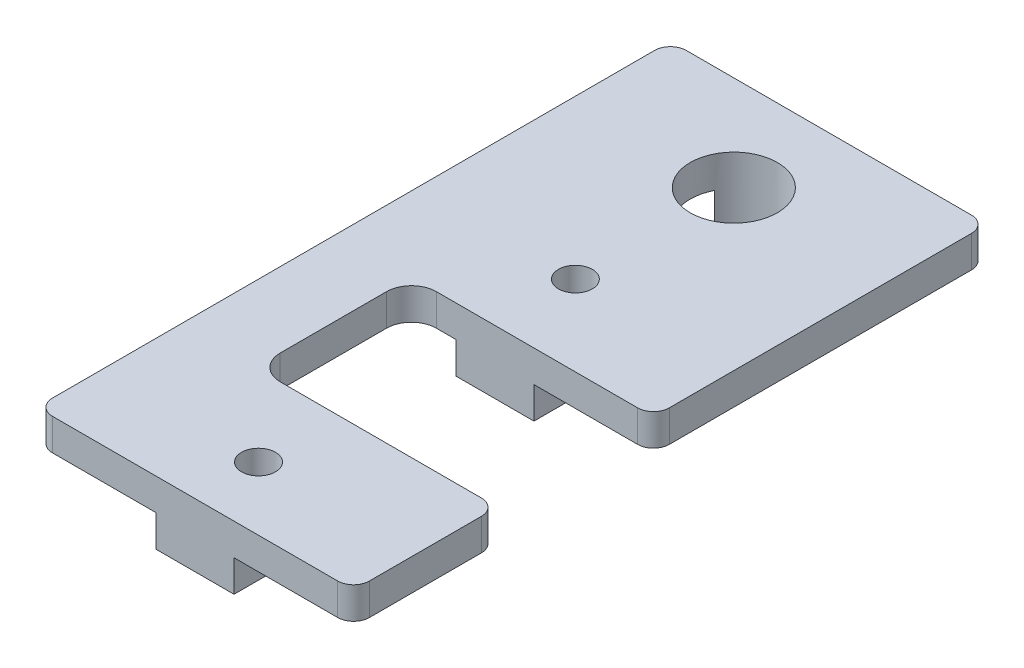
SolidWorks part; units mm, degrees
ref_plane "Front Plane" through (0, 0, 0) normal (0, 0, 1) x (1, 0, 0)
ref_plane "Top Plane" through (0, 0, 0) normal (0, 1, 0) x (1, 0, 0)
ref_plane "Right Plane" through (0, 0, 0) normal (1, 0, 0) x (0, 0, -1)
sketch "Sketch3" plane through (0, 0, 0) normal (0, 0, 1) x (1, 0, 0)
  line L1 (0, 0) -> (31.75, 0)
  line L2 (0, 0) -> (0, 3.175)
  line L3 (0, 3.175) -> (31.75, 3.175)
  line L4 (31.75, 0) -> (31.75, 3.175)
  line L5 (0, 0) -> (31.75, 3.175) construction
  line L6 (0, 3.175) -> (31.75, 0) construction
  line L7 (11.975, 0) -> (19.775, 0)
  line L8 (11.975, 0) -> (11.975, -3.175)
  line L9 (11.975, -3.175) -> (19.775, -3.175)
  line L10 (19.775, 0) -> (19.775, -3.175)
  line L11 (11.975, 0) -> (19.775, -3.175) construction
  line L12 (11.975, -3.175) -> (19.775, 0) construction
  point P4 (15.875, 1.5875)
  point P10 (15.875, -1.5875)
  dimension "D1" = 3.175
  dimension "D2" = 3.175
  dimension "D3" = 7.8
  dimension "D4" = 31.75
extrude "Boss-Extrude2" add sketch "Sketch3" along normal blind 63.5 contours L10 L1 L8 L9 | L1 L4 L3 L2
sketch "Sketch4" plane through (0, 3.175, 0) normal (0, 1, 0) x (1, 0, 0)
  line L0 (0, 0) -> (31.75, 0) construction
  line L1 (0, -63.5) -> (31.75, -63.5) construction
  line L5 (31.75, -63.5) -> (31.75, 0) construction
  line L8 (31.75, -49.1) -> (31.75, -33.45)
  line L9 (0, -63.5) -> (0, 0) construction
  line L10 (31.75, -33.45) -> (10, -33.45)
  line L12 (31.75, -49.1) -> (10, -49.1)
  line L13 (7.5, -35.95) -> (7.5, -46.6)
  circle A0 centre (15.875, -9.525) radius 4.3656
  circle A1 centre (15.875, -25.4) radius 1.7
  circle A2 centre (15.875, -57.15) radius 1.7
  arc A7 (10, -33.45) -> (7.5, -35.95) centre (10, -35.95) ccw
  arc A8 (7.5, -46.6) -> (10, -49.1) centre (10, -46.6) ccw
  point P4 (15.875, 0)
  point P30 (15.875, -27.1)
  point P31 (15.875, -55.45)
  dimension "D2" = 8.7312
  dimension "D3" = 3.4
  dimension "D6" = 2.5
  dimension "D1" = 9.525
  dimension "D4" = 6.35
  dimension "D5" = 31.75
  dimension "D8" = 7.5
  dimension "D11" = 6.35
  dimension "D12" = 6.35
extrude "Cut-Extrude1" cut sketch "Sketch4" against normal through all
fillet "Fillet1" radius 1.5875 6 edges at (31.75, 1.5875, 0) (31.75, 1.5875, 63.5) (0, 1.5875, 63.5) (0, 1.5875, 0) (31.75, 1.5875, 33.45) (31.75, 1.5875, 49.1)
